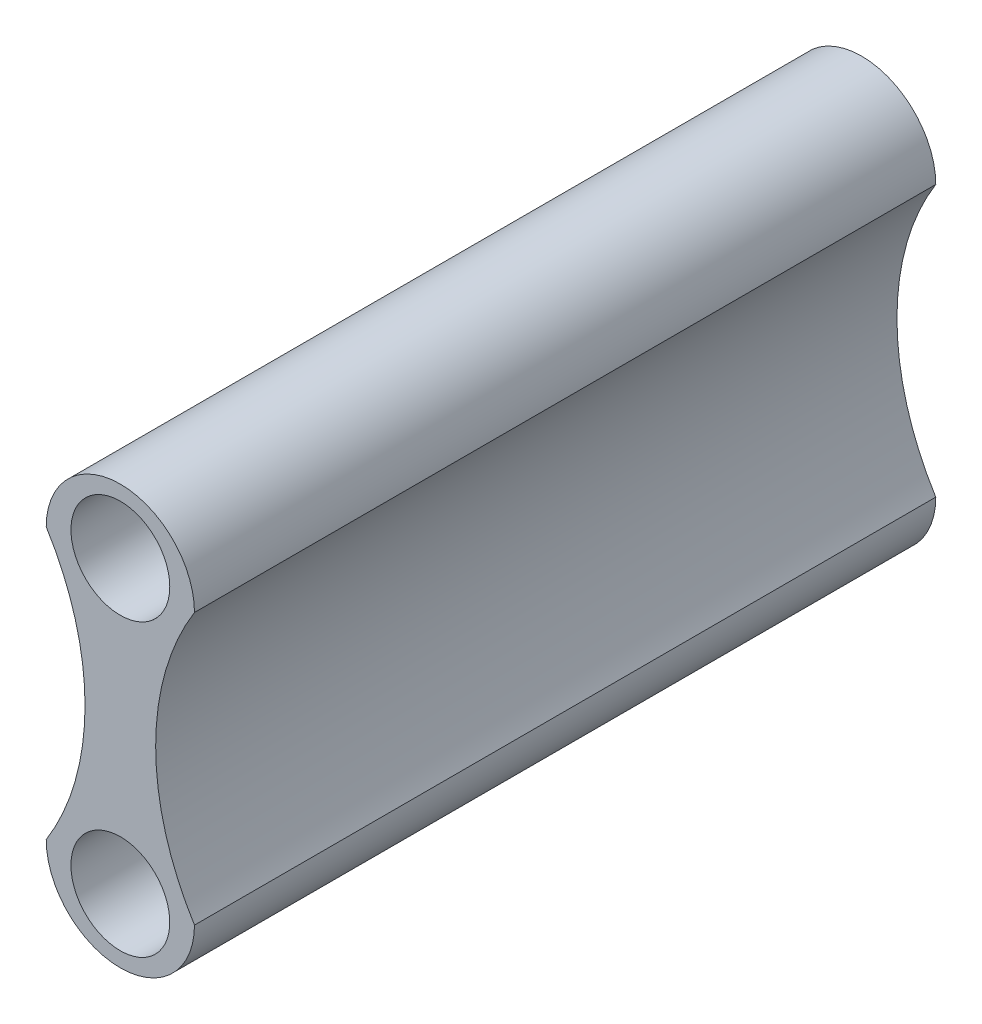
SolidWorks part; units mm, degrees
ref_plane "Front Plane" through (0, 0, 0) normal (0, 0, 1) x (1, 0, 0)
ref_plane "Top Plane" through (0, 0, 0) normal (0, 1, 0) x (1, 0, 0)
ref_plane "Right Plane" through (0, 0, 0) normal (1, 0, 0) x (0, 0, -1)
sketch "Sketch1" plane through (0, 0, 0) normal (0, 0, 1) x (1, 0, 0)
  line L0 (1.5, 0) -> (-1.5, 0) construction
  line L2 (1.5, -2.7394) -> (-1.5, -2.7394) construction
  line L3 (0, -5.4788) -> (0, 0) construction
  arc A0 (1.5, 0) -> (-1.5, 0) centre (0, 0) ccw
  arc A1 (1.5, 0) -> (1.5, -5.4788) centre (5.8846, -2.7394) ccw
  arc A2 (1.5, -5.4788) -> (-1.5, -5.4788) centre (0, -5.4788) cw
  arc A3 (-1.5, 0) -> (-1.5, -5.4788) centre (-5.8846, -2.7394) cw
  dimension "D1" = 3
  dimension "D2" = 10.34
extrude "Boss-Extrude1" add sketch "Sketch1" along normal blind 15
sketch "Sketch2" plane through (0, 0, 15) normal (0, 0, 1) x (1, 0, 0)
  line L0 (0, 0) -> (0, 0.2) construction
  line L1 (-0.7146, -2.7394) -> (0.7146, -2.7394) construction
  arc A1 (-1.5, -5.4788) -> (-1.5, 0) centre (-5.8846, -2.7394) ccw construction
  circle A3 centre (0, 0.2) radius 1
  arc A4 (1.5, 0) -> (1.5, -5.4788) centre (5.8846, -2.7394) ccw construction
  circle A5 centre (0, -5.6788) radius 1
  dimension "D1" = 2
  dimension "D2" = 0.2
extrude "Cut-Extrude1" cut sketch "Sketch2" against normal blind 4
sketch "Sketch3" plane through (0, 0, 0) normal (0, 0, -1) x (-1, 0, 0)
  circle A0 centre (0, 0.2) radius 1 construction
  circle A1 centre (0, 0.2) radius 1
  circle A2 centre (0, -5.6788) radius 1 construction
  circle A3 centre (0, -5.6788) radius 1
extrude "Cut-Extrude2" cut sketch "Sketch3" against normal blind 4
